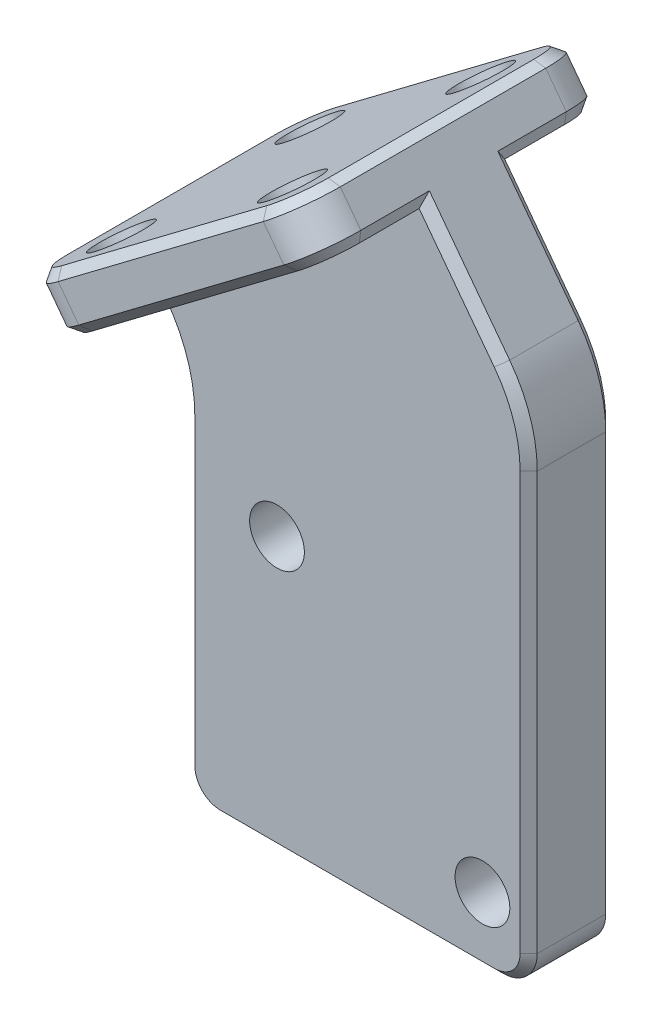
SolidWorks part; units mm, degrees
material "6061-T6 (SS)"
ref_plane "前视基准面" through (0, 0, 0) normal (0, 0, 1) x (1, 0, 0)
ref_plane "上视基准面" through (0, 0, 0) normal (0, 1, 0) x (1, 0, 0)
ref_plane "右视基准面" through (0, 0, 0) normal (1, 0, 0) x (0, 0, -1)
sketch "草图1" plane through (0, 0, 0) normal (0, 0, 1) x (1, 0, 0)
  line L0 (0, 2) -> (0, 19.7054)
  line L1 (-1.6109, 24.5199) -> (-1.9727, 25)
  line L2 (-1.9727, 25) -> (14, 37.0363)
  line L3 (14, 37.0363) -> (18.3891, 31.2118)
  line L4 (20, 26.3973) -> (20, 2)
  line L5 (18, 0) -> (2, 0)
  circle A0 centre (5.3, 16) radius 1.6
  circle A1 centre (17.3, 4) radius 1.6
  arc A2 (20, 2) -> (18, 0) centre (18, 2) cw
  arc A3 (0, 2) -> (2, 0) centre (2, 2) ccw
  arc A4 (18.3891, 31.2118) -> (20, 26.3973) centre (12, 26.3973) cw
  arc A5 (0, 19.7054) -> (-1.6109, 24.5199) centre (-8, 19.7054) ccw
  point P15 (20, 0)
  point P18 (0, 0)
  dimension "D2" = 12
  dimension "D3" = 12
  dimension "D4" = 5.3
  dimension "D5" = 4
  dimension "D6" = 3.2
  dimension "D11" = 2
  dimension "D12" = 8
  dimension "D1" = 20
  dimension "D7" = 37
  dimension "D8" = 20
  dimension "D9" = 25
  dimension "D10" = 6
extrude "凸台-拉伸1" add sketch "草图1" along normal blind 5
sketch "草图2" plane through (-12.7302, 16.8936, 0) normal (-0.6018, 0.7986, 0) x (0.7986, 0.6018, 0)
  line L0 (23.4699, 0) -> (23.4699, -2.5) construction
  line L1 (30.9699, -11) -> (15.9699, -11)
  line L2 (33.4699, -8.5) -> (33.4699, 3.5)
  line L3 (30.9699, 6) -> (15.9699, 6)
  line L4 (13.4699, -8.5) -> (13.4699, 3.5)
  line L5 (33.4699, -11) -> (13.4699, 6) construction
  line L6 (33.4699, 6) -> (13.4699, -11) construction
  line L7 (33.4699, 0) -> (13.4699, 0) construction
  line L8 (23.4699, -2.5) -> (13.4699, -2.5) construction
  line L9 (13.4699, -5) -> (13.4699, 0) construction
  line L10 (33.4699, -5) -> (33.4699, 0) construction
  line L12 (29.7199, -8) -> (17.2199, -8) construction
  line L13 (29.7199, -8) -> (29.7199, 3) construction
  line L14 (29.7199, 3) -> (17.2199, 3) construction
  line L15 (17.2199, -8) -> (17.2199, 3) construction
  line L16 (29.7199, -8) -> (17.2199, 3) construction
  line L17 (29.7199, 3) -> (17.2199, -8) construction
  arc A0 (15.9699, -11) -> (13.4699, -8.5) centre (15.9699, -8.5) cw
  arc A1 (33.4699, 3.5) -> (30.9699, 6) centre (30.9699, 3.5) ccw
  arc A2 (30.9699, -11) -> (33.4699, -8.5) centre (30.9699, -8.5) ccw
  arc A3 (15.9699, 6) -> (13.4699, 3.5) centre (15.9699, 3.5) ccw
  circle A4 centre (17.2199, 3) radius 1.6
  circle A5 centre (29.7199, 3) radius 1.6
  circle A6 centre (29.7199, -8) radius 1.6
  circle A7 centre (17.2199, -8) radius 1.6
  point P0 (23.4699, -2.5)
  dimension "D2" = 2.5
  dimension "D5" = 3.2
  dimension "D1" = 17
  dimension "D3" = 12.5
  dimension "D4" = 11
extrude "凸台-拉伸2" add sketch "草图2" along normal blind 3
chamfer "倒角1" distance 0.5 angle 45 36 edges at (4.2082, 33.4141, 11) (11.6098, 38.9915, 10.2678) (-3.1934, 27.8366, 10.2678) (12.1946, 39.4322, 2.5) (-3.7782, 27.3959, 2.5) (11.6098, 38.9915, -5.2678) (-3.1934, 27.8366, -5.2678) (4.2082, 33.4141, -6) (14, 37.0363, -1.75) (-1.9727, 25, -1.75) (13.4152, 36.5956, -5.2678) (-1.3879, 25.4407, -5.2678) (6.0136, 31.0182, -6) (-1.9727, 25, 6.75) (14, 37.0363, 6.75) (-1.3879, 25.4407, 10.2678) (13.4152, 36.5956, 10.2678) (6.0136, 31.0182, 11) (16.1945, 34.124, 0) (19.5866, 28.9357, 0) (20, 14.1986, 0) (19.4142, 0.5858, 0) (-1.7918, 24.7599, 0) (10, 0, 0) (-0.4134, 22.2438, 0) (0.5858, 0.5858, 0) (0, 10.8527, 0) (16.1945, 34.124, 5) (19.5866, 28.9357, 5) (20, 14.1986, 5) (19.4142, 0.5858, 5) (-1.7918, 24.7599, 5) (10, 0, 5) (-0.4134, 22.2438, 5) (0.5858, 0.5858, 5) (0, 10.8527, 5)
